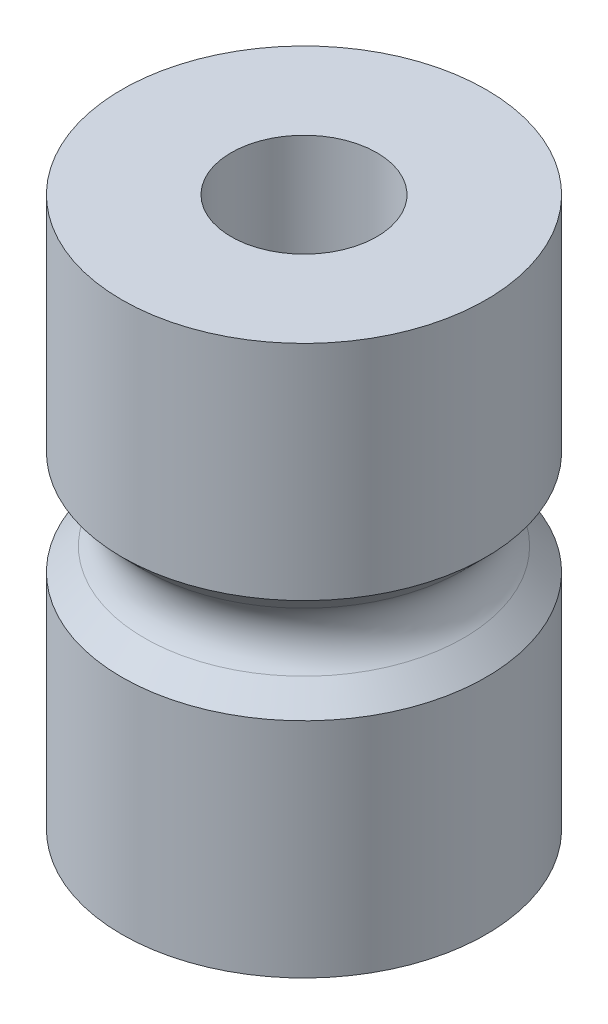
SolidWorks part; units mm, degrees
ref_plane "Front Plane" through (0, 0, 0) normal (0, 0, 1) x (1, 0, 0)
ref_plane "Top Plane" through (0, 0, 0) normal (0, 1, 0) x (1, 0, 0)
ref_plane "Right Plane" through (0, 0, 0) normal (1, 0, 0) x (0, 0, -1)
sketch "Sketch2" plane through (0, 0, 0) normal (0, 0, 1) x (1, 0, 0)
  line L0 (0, 0) -> (4.445, 0) construction
  line L1 (16.7951, 0) -> (16.7951, 16.764) construction
  line L2 (4.445, 0) -> (11.1125, 0)
  line L3 (4.445, 0) -> (4.445, 33.528)
  line L4 (4.445, 33.528) -> (11.1125, 33.528)
  line L5 (11.1125, 0) -> (11.1125, 13.589)
  line L6 (7.9375, 16.764) -> (11.1125, 13.589)
  line L7 (7.9375, 16.764) -> (11.1125, 19.939)
  line L8 (11.1125, 19.939) -> (11.1125, 33.528)
  line L9 (0, 0) -> (0, 30.073) construction
  point P9 (0, 0)
  dimension "D1" = 4.445
  dimension "D2" = 33.528
  dimension "D3" = 11.1125
  dimension "D4" = 16.764
  dimension "D5" = 3.175
  dimension "D6" = 45
  dimension "D7" = 6.35
revolve "Revolve1" add sketch "Sketch2" angle 360 about L9
fillet "Fillet1" radius 2.54 1 edges at (0, 16.764, -7.9375)
